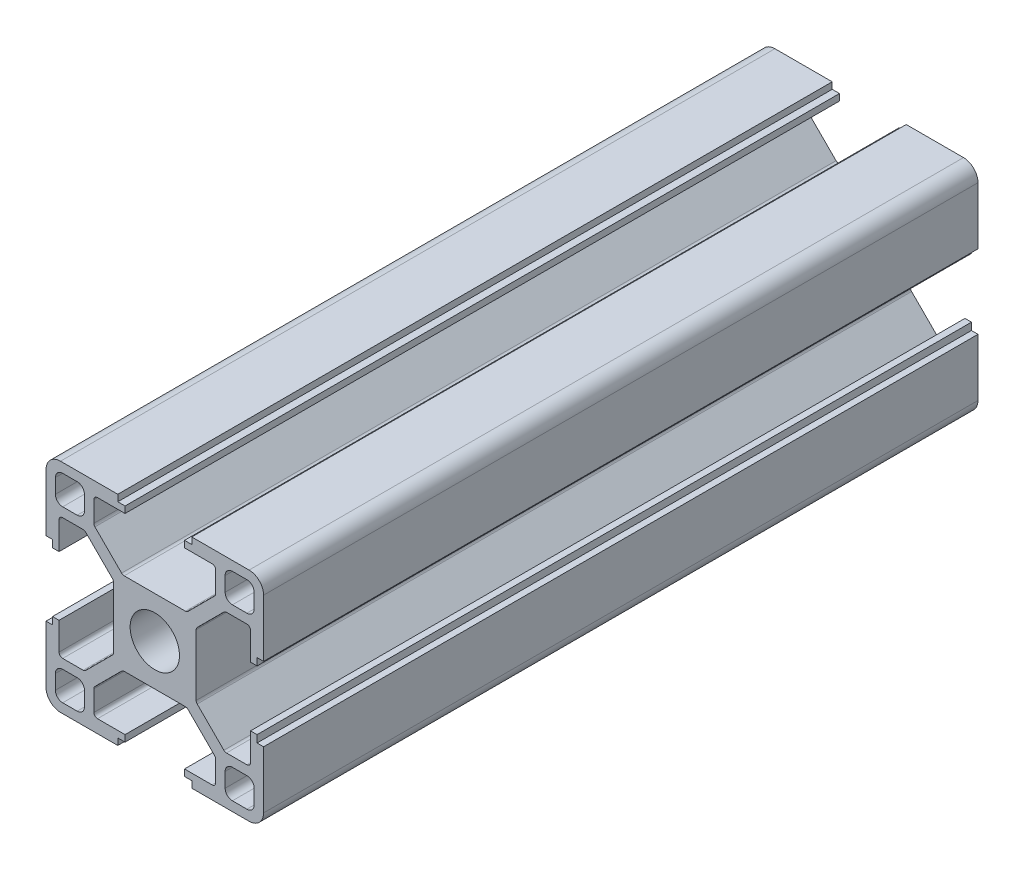
SolidWorks part; units mm, degrees
ref_plane "前视基准面" through (0, 0, 0) normal (0, 0, 1) x (1, 0, 0)
ref_plane "上视基准面" through (0, 0, 0) normal (0, 1, 0) x (1, 0, 0)
ref_plane "右视基准面" through (0, 0, 0) normal (1, 0, 0) x (0, 0, -1)
sketch "草图1" plane through (0, 0, 0) normal (0, 0, 1) x (1, 0, 0)
  line L0 (0, 0) -> (0, 65.3905) construction
  line L1 (0, 0) -> (64.2648, 0) construction
  line L2 (0, 0) -> (79.9729, 79.9729) construction
  line L3 (5.7, 0) -> (5.7, 4.4272)
  line L4 (5.7, 4.4272) -> (9.6728, 8.4)
  line L5 (9.6728, 8.4) -> (13.2, 8.4)
  line L6 (13.2, 8.4) -> (13.2, 4.1)
  line L7 (13.2, 4.1) -> (14.1, 4.1)
  line L8 (14.1, 4.1) -> (14.1, 5.1)
  line L9 (14.1, 5.1) -> (15, 5.1)
  line L10 (15, 5.1) -> (15, 15)
  line L11 (5.1, 15) -> (15, 15)
  line L12 (5.1, 14.1) -> (5.1, 15)
  line L13 (4.1, 14.1) -> (5.1, 14.1)
  line L14 (4.1, 13.2) -> (4.1, 14.1)
  line L15 (8.4, 13.2) -> (4.1, 13.2)
  line L16 (8.4, 9.6728) -> (8.4, 13.2)
  line L17 (4.4272, 5.7) -> (8.4, 9.6728)
  line L18 (0, 5.7) -> (4.4272, 5.7)
  line L20 (9.7, 9.7) -> (13.7, 9.7)
  line L21 (9.7, 9.7) -> (9.7, 13.7)
  line L22 (9.7, 13.7) -> (13.7, 13.7)
  line L23 (13.7, 9.7) -> (13.7, 13.7)
  line L24 (9.7, 9.7) -> (13.7, 13.7) construction
  line L25 (9.7, 13.7) -> (13.7, 9.7) construction
  line L26 (0, 5.7) -> (0, 0)
  line L27 (0, 0) -> (5.7, 0)
  point P9 (11.7, 11.7)
  dimension "D1" = 45
  dimension "D2" = 5.7
  dimension "D3" = 1.8
  dimension "D4" = 0.9
  dimension "D5" = 8.2
  dimension "D6" = 10.2
  dimension "D7" = 1.8
  dimension "D8" = 15
  dimension "D9" = 16.8
  dimension "D10" = 4
  dimension "D11" = 1.3
extrude "凸台-拉伸1" add sketch "草图1" along normal blind 98.5 contours L3 L4 L5 L6 L7 L8 L9 L10 L11 L12 L13 L14 L15 L16 L17 L18 L26 L27
fillet "圆角1" radius 1 4 edges at (9.7, 9.7, 49.25) (13.7, 9.7, 49.25) (9.7, 13.7, 49.25) (13.7, 13.7, 49.25)
fillet "圆角2" radius 2 1 edges at (15, 15, 49.25)
fillet "圆角3" radius 0.5 6 edges at (5.7, 4.4272, 49.25) (4.4272, 5.7, 49.25) (8.4, 13.2, 49.25) (8.4, 9.6728, 49.25) (9.6728, 8.4, 49.25) (13.2, 8.4, 49.25)
pattern_circular "阵列(圆周)1" count 4 over 360 about axis through (0, 0, 0) along (0, 0, 1) of "圆角2", "圆角3", "凸台-拉伸1", "圆角1"
sketch "草图2" plane through (0, 0, 98.5) normal (0, 0, 1) x (1, 0, 0)
  circle A0 centre (0, 0) radius 3.4
  dimension "D1" = 6.8
extrude "切除-拉伸1" cut sketch "草图2" against normal through all
sketch "草图3" plane through (0, 0, 0) normal (0, 1, 0) x (1, 0, 0)
  line L0 (0, 29.4599) -> (0, -128.6575) construction
  line L1 (4.2201, -98.5) -> (-4.2201, -98.5) construction
  circle A0 centre (0, -58.5) radius 2.75
  circle A1 centre (0, -78.5) radius 2.75
  dimension "D1" = 20
  dimension "D3" = 5.5
  dimension "D2" = 20
extrude "切除-拉伸2" cut sketch "草图3" against normal mid plane 1060
